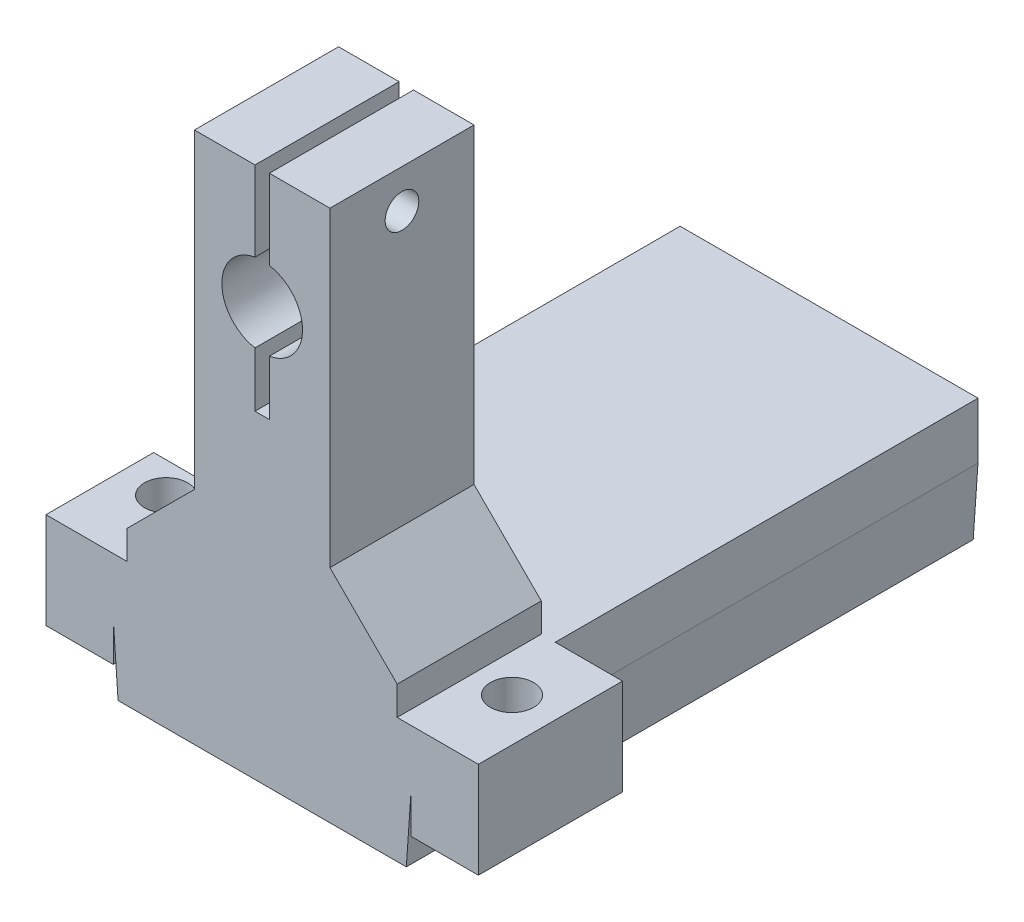
SolidWorks part; units mm, degrees
ref_plane "Front Plane" through (0, 0, 0) normal (0, 0, 1) x (1, 0, 0)
ref_plane "Top Plane" through (0, 0, 0) normal (0, 1, 0) x (1, 0, 0)
ref_plane "Right Plane" through (0, 0, 0) normal (1, 0, 0) x (0, 0, -1)
sketch "Sketch1" plane through (0, 0, 0) normal (0, 1, 0) x (1, 0, 0)
  line L0 (-23, 32) -> (-23, 22)
  line L1 (0, 0) -> (-26, 0)
  line L2 (0, 0) -> (0, 53)
  line L3 (0, 53) -> (-26, 53)
  line L4 (-26, 0) -> (-26, 53)
  line L5 (-23, 48) -> (-3, 48)
  line L6 (-23, 48) -> (-23, 38)
  line L7 (-23, 38) -> (-3, 38)
  line L8 (-3, 48) -> (-3, 38)
  line L9 (-23, 32) -> (-3, 32)
  line L10 (-3, 32) -> (-3, 22)
  line L11 (-23, 22) -> (-3, 22)
  line L12 (-23, 16) -> (-23, 6)
  line L13 (-23, 16) -> (-3, 16)
  line L14 (-3, 16) -> (-3, 6)
  line L15 (-23, 6) -> (-3, 6)
  point P9 (-13, 48)
  point P10 (-13, 53)
  dimension "D1" = 26
  dimension "D2" = 53
  dimension "D3" = 20
  dimension "D4" = 10
  dimension "D5" = 5
  dimension "D6" = 3
extrude "Boss-Extrude1" add sketch "Sketch1" along normal blind 5
sketch "Sketch2" plane through (0, 5, 0) normal (0, 1, 0) x (1, 0, 0)
  line L17 (-26, 53) -> (0, 53)
  line L18 (-26, 53) -> (-26, 0)
  line L19 (-26, 0) -> (0, 0)
  line L20 (0, 53) -> (0, 0)
  line L21 (-28.5, 56) -> (2.5, 56)
  line L22 (-28.5, 56) -> (-28.5, -3)
  line L23 (-28.5, -3) -> (2.5, -3)
  line L24 (2.5, 56) -> (2.5, -3)
  dimension "D1" = 3
  dimension "D2" = 2.5
  dimension "D3" = 2.5
  dimension "D4" = 3
extrude "Boss-Extrude2" add sketch "Sketch2" against normal blind 10
sketch "Sketch3" plane through (0, 5, 0) normal (0, 1, 0) x (1, 0, 0)
  line L1 (-28.5, 56) -> (2.5, 56)
  line L2 (-28.5, 56) -> (-28.5, -3)
  line L3 (-28.5, -3) -> (2.5, -3)
  line L4 (2.5, 56) -> (2.5, -3)
extrude "Boss-Extrude3" add sketch "Sketch3" along normal blind 3
sketch "Sketch4" plane through (0, 8, 0) normal (0, 1, 0) x (1, 0, 0)
  line L1 (-5, 56) -> (-11, 56)
  line L2 (-5, 56) -> (-5, 10)
  line L3 (-5, 10) -> (-11, 10)
  line L4 (-11, 56) -> (-11, 10)
  line L6 (-3, 38) -> (-3, 48) construction
  line L8 (-28.5, -3) -> (2.5, -3) construction
  dimension "D1" = 6
  dimension "D2" = 2
  dimension "D3" = 46
  dimension "D4" = 13
extrude "Boss-Extrude4" [suppressed] add sketch "Sketch4" along normal blind 55
sketch "Sketch5" [suppressed] plane through (-5, 0, 0) normal (1, 0, 0) x (0, 0, -1)
  line L0 (10, 8) -> (56, 8) construction
  line L1 (56, 63) -> (56, 8) construction
  line L2 (19, 48) -> (50, 17) construction
  line L3 (50, 48) -> (19, 17) construction
  circle A0 centre (50, 17) radius 1.75
  circle A1 centre (19, 17) radius 1.75
  circle A2 centre (19, 48) radius 1.75
  circle A3 centre (50, 48) radius 1.75
  circle A4 centre (34.5, 32.5) radius 13.5
  dimension "D2" = 6
  dimension "D3" = 3.5
  dimension "D6" = 27
  dimension "D1" = 9
  dimension "D4" = 2
  dimension "D5" = 2
extrude "Cut-Extrude1" [suppressed] cut sketch "Sketch5" against normal through all
chamfer "Chamfer1" distance 0.5 angle 86 2 edges at (2.5, -5, -26.5) (-28.5, -5, -26.5)
sketch "Sketch6" [suppressed] plane through (-5, 0, 0) normal (1, 0, 0) x (0, 0, -1)
  line L0 (10, 63) -> (10, 8) construction
  line L1 (56, 63) -> (10, 63)
  line L2 (56, 63) -> (56, 56)
  line L3 (56, 56) -> (10, 56)
  line L4 (10, 63) -> (10, 56)
  dimension "D1" = 7
extrude "Boss-Extrude5" [suppressed] add sketch "Sketch6" along normal blind 14
sketch "Sketch7" [suppressed] plane through (0, 63, 0) normal (0, 1, 0) x (1, 0, 0)
  line L0 (-11, 56) -> (-11, 10) construction
  line L1 (-8.5, 39.5) -> (-3.5, 39.5)
  line L2 (-8.5, 39.5) -> (-8.5, 34.5)
  line L3 (-8.5, 34.5) -> (-3.5, 34.5)
  line L4 (-3.5, 39.5) -> (-3.5, 34.5)
  line L5 (1.5, 39.5) -> (6.5, 39.5)
  line L6 (1.5, 39.5) -> (1.5, 34.5)
  line L7 (1.5, 34.5) -> (6.5, 34.5)
  line L8 (6.5, 39.5) -> (6.5, 34.5)
  line L9 (-8.5, 16.5) -> (-3.5, 16.5)
  line L10 (-8.5, 16.5) -> (-8.5, 11.5)
  line L11 (-8.5, 11.5) -> (-3.5, 11.5)
  line L12 (-3.5, 16.5) -> (-3.5, 11.5)
  line L13 (1.5, 16.5) -> (6.5, 16.5)
  line L14 (1.5, 16.5) -> (1.5, 11.5)
  line L15 (1.5, 11.5) -> (6.5, 11.5)
  line L16 (6.5, 16.5) -> (6.5, 11.5)
  line L17 (-11, 10) -> (9, 10) construction
  point P18 (-6, 16.5)
  point P19 (-6, 39.5)
  point P20 (4, 39.5)
  point P21 (4, 16.5)
  point P22 (-3.5, 37)
  point P23 (1.5, 37)
  point P24 (-3.5, 14)
  point P25 (1.5, 14)
  dimension "D1" = 5
  dimension "D2" = 5
  dimension "D3" = 2.5
  dimension "D4" = 1.5
  dimension "D5" = 23
extrude "Cut-Extrude2" [suppressed] cut sketch "Sketch7" against normal blind 5
sketch "Sketch8" [suppressed] plane through (0, 0, -56) normal (0, 0, -1) x (-1, 0, 0)
  line L0 (-9, 56) -> (-9, 63) construction
  line L1 (-9, 8) -> (5.6893, 8)
  line L2 (-9, 8) -> (-9, 1)
  line L3 (-9, 1) -> (5.6893, 1)
  line L4 (5.6893, 8) -> (5.6893, 1)
  line L5 (-2.5, 8) -> (5, 8) construction
extrude "Boss-Extrude6" [suppressed] add sketch "Sketch8" against normal blind 7.5
sketch "Sketch9" [suppressed] plane through (0, 0, -56) normal (0, 0, -1) x (-1, 0, 0)
  line L0 (-9, 56) -> (-9, 63) construction
  line L1 (-9, 8) -> (-9, 1) construction
  line L2 (11, 63) -> (11, 8) construction
  line L3 (5, 56) -> (5, 8) construction
  line L4 (-9, 8) -> (5, 8) construction
  line L6 (-9, 56) -> (5, 56) construction
  circle A0 centre (-5.5, 59.5) radius 1.75
  circle A1 centre (-5.5, 4.5) radius 1.75
  circle A2 centre (8, 54) radius 1.75
  circle A3 centre (8, 10) radius 1.75
  circle A4 centre (8, 32) radius 1.75
  point P5 (-9, 59.5)
  point P9 (-9, 4.5)
  dimension "D1" = 3.5
  dimension "D2" = 3.5
  dimension "D3" = 3.5
  dimension "D4" = 3.5
  dimension "D5" = 3
  dimension "D6" = 3
  dimension "D7" = 3
  dimension "D8" = 2
  dimension "D9" = 2
  dimension "D10" = 22
  dimension "D11" = 22
extrude "Cut-Extrude3" [suppressed] cut sketch "Sketch9" against normal blind 4
sketch "Sketch10" plane through (0, 8, 0) normal (0, 1, 0) x (1, 0, 0)
  line L0 (-13, -3) -> (-13, 56) construction
  line L1 (2.5, -3) -> (9.5, -3)
  line L2 (2.5, -3) -> (2.5, 12)
  line L3 (2.5, 12) -> (9.5, 12)
  line L4 (9.5, -3) -> (9.5, 12)
  line L9 (-28.5, -3) -> (2.5, -3) construction
  line L10 (2.5, 56) -> (-28.5, 56) construction
  line L11 (-28.5, 12) -> (-35.5, 12)
  line L12 (-35.5, -3) -> (-35.5, 12)
  line L13 (-28.5, -3) -> (-35.5, -3)
  line L14 (-28.5, -3) -> (-28.5, 12)
  circle A0 centre (5, 5) radius 2.25
  circle A1 centre (-31, 5) radius 2.25
  dimension "D6" = 4.5
  dimension "D3" = 4.5
  dimension "D1" = 15
  dimension "D2" = 7
  dimension "D5" = 8
extrude "Boss-Extrude7" add sketch "Sketch10" against normal blind 10
sketch "Sketch11" plane through (0, 0, 0) normal (0, 0, 1) x (1, 0, 0)
  line L0 (-35.5, 8) -> (9.5, 8) construction
  line L2 (-35.5, -2) -> (-35.5, 8) construction
  line L3 (9.5, -2) -> (9.5, 8) construction
  line L7 (-13.7486, 28.199) -> (-12.2514, 28.199)
  line L28 (-13.7486, 42.0905) -> (-13.7486, 50.4)
  line L29 (-13.7486, 50.4) -> (-20.0486, 50.4)
  line L30 (-20.0486, 50.4) -> (-20.0486, 18)
  line L31 (-20.0486, 18) -> (-27.0486, 11)
  line L32 (-27.0486, 11) -> (-27.0486, 8)
  line L33 (-27.0486, 8) -> (1.0486, 8)
  line L34 (1.0486, 8) -> (1.0486, 11)
  line L35 (1.0486, 11) -> (-5.9514, 18)
  line L36 (-5.9514, 18) -> (-5.9514, 50.4)
  line L37 (-5.9514, 50.4) -> (-12.2514, 50.4)
  line L38 (-12.2514, 50.4) -> (-12.2514, 42.0905)
  line L39 (-12.2514, 33.9095) -> (-12.2514, 28.199)
  line L41 (-13.7486, 28.199) -> (-13.7486, 33.9095)
  arc A4 (-12.2514, 33.9095) -> (-12.2514, 42.0905) centre (-12.9514, 38) ccw
  arc A5 (-13.7486, 42.0905) -> (-13.7486, 33.9095) centre (-13.0486, 38) ccw
  dimension "D1" = 8.4514
  dimension "D2" = 8.4514
extrude "Boss-Extrude9" add sketch "Sketch11" along normal up to surface (3 mm away) and the other way blind 12 up to face at (-13, 0.2301, 3)
sketch "Sketch12" plane through (-5.9514, 0, 0) normal (1, 0, 0) x (0, 0, -1)
  line L0 (12, 50.4) -> (-3, 50.4) construction
  circle A0 centre (4.5, 46.4) radius 1.75
  point P5 (4.5, 50.4)
  dimension "D1" = 3.5
  dimension "D2" = 4
extrude "Cut-Extrude4" cut sketch "Sketch12" against normal through all
sketch "Sketch13" plane through (0, 8, 0) normal (0, 1, 0) x (1, 0, 0)
  line L1 (-35.5, 12) -> (-28.5, 12)
  line L2 (-35.5, 12) -> (-35.5, 8.2)
  line L3 (-35.5, 8.2) -> (-28.5, 8.2)
  line L4 (-28.5, 12) -> (-28.5, 8.2)
  dimension "D1" = 3.8
extrude "Cut-Extrude5" cut sketch "Sketch13" against normal blind 10
